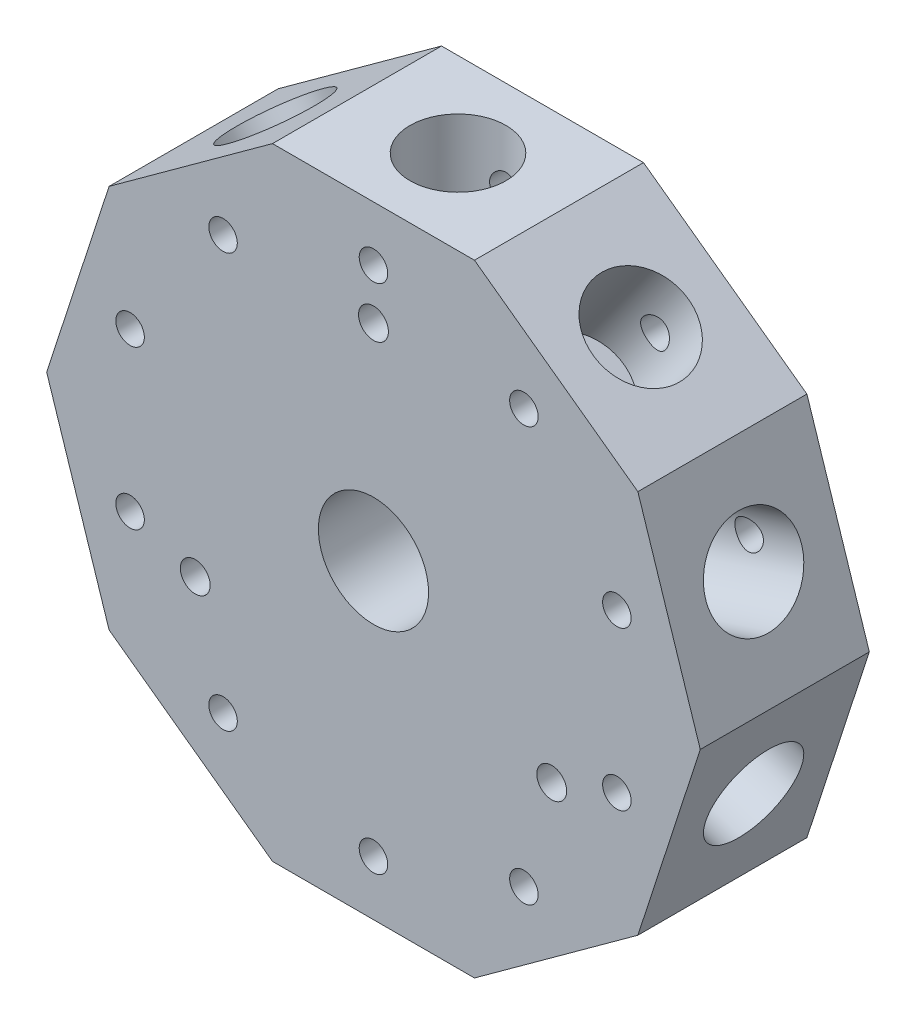
SolidWorks part; units mm, degrees
material "6061-T6 (SS)"
ref_plane "Front Plane" through (0, 0, 0) normal (0, 0, 1) x (1, 0, 0)
ref_plane "Top Plane" through (0, 0, 0) normal (0, 1, 0) x (1, 0, 0)
ref_plane "Right Plane" through (0, 0, 0) normal (1, 0, 0) x (0, 0, -1)
sketch "Sketch1" plane through (0, 0, 0) normal (0, 0, 1) x (1, 0, 0)
  line L1 (30.5891, 22.2243) -> (11.684, 35.9597)
  line L2 (11.684, 35.9597) -> (-11.684, 35.9597)
  line L3 (-11.684, 35.9597) -> (-30.5891, 22.2243)
  line L4 (-30.5891, 22.2243) -> (-37.8102, 0)
  line L5 (-37.8102, 0) -> (-30.5891, -22.2243)
  line L6 (-30.5891, -22.2243) -> (-11.684, -35.9597)
  line L7 (-11.684, -35.9597) -> (11.684, -35.9597)
  line L8 (11.684, -35.9597) -> (30.5891, -22.2243)
  line L9 (30.5891, -22.2243) -> (37.8102, 0)
  line L10 (37.8102, 0) -> (30.5891, 22.2243)
  circle A0 centre (0, 0) radius 37.8102 construction
  dimension "D1" = 23.368
extrude "Boss-Extrude1" add sketch "Sketch1" against normal blind 19.558
sketch "Sketch5" plane through (0, 35.9597, 0) normal (0, 1, 0) x (1, 0, 0)
  line L0 (11.684, 0) -> (-11.684, 0) construction
  line L1 (11.684, 19.558) -> (11.684, 0) construction
  circle A0 centre (0, 9.779) radius 5.5499
  dimension "D2" = 11.0998
  dimension "D1" = 9.779
  dimension "D3" = 11.684
extrude "Cut-Extrude3" cut sketch "Sketch5" against normal blind 12.7
sketch "Sketch6" plane through (21.1366, 29.092, 0) normal (0.5878, 0.809, 0) x (0.809, -0.5878, 0)
  line L0 (11.684, 0) -> (-11.684, 0) construction
  line L1 (11.684, 19.558) -> (11.684, 0) construction
  circle A0 centre (0, 9.779) radius 5.5499
  dimension "D2" = 11.0998
  dimension "D1" = 9.779
  dimension "D3" = 11.684
extrude "Cut-Extrude4" cut sketch "Sketch6" against normal blind 12.7
sketch "Sketch7" plane through (34.1997, 11.1121, 0) normal (0.9511, 0.309, 0) x (0, 0, -1)
  line L0 (0, -11.684) -> (0, 11.684) construction
  line L1 (19.558, -11.684) -> (0, -11.684) construction
  circle A0 centre (9.779, 0) radius 5.5499
  dimension "D2" = 11.0998
  dimension "D1" = 9.779
  dimension "D3" = 11.684
extrude "Cut-Extrude5" cut sketch "Sketch7" against normal blind 12.7
sketch "Sketch8" plane through (34.1997, -11.1121, 0) normal (0.9511, -0.309, 0) x (0, 0, -1)
  line L0 (0, -11.684) -> (0, 11.684) construction
  line L1 (19.558, -11.684) -> (0, -11.684) construction
  circle A0 centre (9.779, 0) radius 5.5499
  dimension "D2" = 11.0998
  dimension "D1" = 9.779
  dimension "D3" = 11.684
extrude "Cut-Extrude6" cut sketch "Sketch8" against normal blind 12.7
sketch "Sketch9" plane through (21.1366, -29.092, 0) normal (0.5878, -0.809, 0) x (0.809, 0.5878, 0)
  line L0 (-11.684, 0) -> (11.684, 0) construction
  line L1 (-11.684, -19.558) -> (-11.684, 0) construction
  circle A0 centre (0, -9.779) radius 5.5499
  dimension "D2" = 11.0998
  dimension "D1" = 9.779
  dimension "D3" = 11.684
extrude "Cut-Extrude7" cut sketch "Sketch9" against normal blind 12.7
sketch "Sketch10" plane through (0, -35.9597, 0) normal (0, -1, 0) x (1, 0, 0)
  line L0 (-11.684, 0) -> (11.684, 0) construction
  line L1 (-11.684, -19.558) -> (-11.684, 0) construction
  circle A0 centre (0, -9.779) radius 5.5499
  dimension "D2" = 11.0998
  dimension "D1" = 9.779
  dimension "D3" = 11.684
extrude "Cut-Extrude8" cut sketch "Sketch10" against normal blind 12.7
sketch "Sketch11" plane through (-21.1366, -29.092, 0) normal (-0.5878, -0.809, 0) x (0.809, -0.5878, 0)
  line L0 (-11.684, 0) -> (11.684, 0) construction
  line L1 (-11.684, -19.558) -> (-11.684, 0) construction
  circle A0 centre (0, -9.779) radius 5.5499
  dimension "D2" = 11.0998
  dimension "D1" = 9.779
  dimension "D3" = 11.684
extrude "Cut-Extrude9" cut sketch "Sketch11" against normal blind 12.7
sketch "Sketch12" plane through (-34.1997, -11.1121, 0) normal (-0.9511, -0.309, 0) x (0, 0, 1)
  line L0 (0, 11.684) -> (0, -11.684) construction
  line L1 (-19.558, 11.684) -> (0, 11.684) construction
  circle A0 centre (-9.779, 0) radius 5.5499
  dimension "D2" = 11.0998
  dimension "D1" = 9.779
  dimension "D3" = 11.684
extrude "Cut-Extrude10" cut sketch "Sketch12" against normal blind 12.7
sketch "Sketch13" plane through (-34.1997, 11.1121, 0) normal (-0.9511, 0.309, 0) x (0, 0, 1)
  line L0 (0, 11.684) -> (0, -11.684) construction
  line L1 (-19.558, 11.684) -> (0, 11.684) construction
  circle A0 centre (-9.779, 0) radius 5.5499
  dimension "D2" = 11.0998
  dimension "D1" = 9.779
  dimension "D3" = 11.684
extrude "Cut-Extrude11" cut sketch "Sketch13" against normal blind 12.7
sketch "Sketch14" plane through (-21.1366, 29.092, 0) normal (-0.5878, 0.809, 0) x (0.809, 0.5878, 0)
  line L0 (11.684, 0) -> (-11.684, 0) construction
  circle A0 centre (0, 9.779) radius 5.5499
  dimension "D2" = 11.0998
  dimension "D1" = 9.779
extrude "Cut-Extrude12" cut sketch "Sketch14" against normal blind 12.7
sketch "Sketch16" plane through (0, 0, 0) normal (0, 0, 1) x (1, 0, 0)
  circle A0 centre (0, 0) radius 9.525
  dimension "D1" = 19.05
extrude "Boss-Extrude2" add sketch "Sketch16" along normal blind 12.7
sketch "Sketch17" plane through (0, 0, 12.7) normal (0, 0, 1) x (1, 0, 0)
  circle A0 centre (0, 0) radius 6.3754
  dimension "D1" = 12.7508
extrude "Cut-Extrude13" cut sketch "Sketch17" against normal blind 15.24
sketch "Sketch18" plane through (0, 0, 0) normal (0, 0, 1) x (1, 0, 0)
  line L0 (11.684, 35.9597) -> (-11.684, 35.9597) construction
  circle A0 centre (0, 29.6097) radius 1.632
  circle A1 centre (17.4041, 23.9547) radius 1.632
  circle A2 centre (28.1605, 9.1499) radius 1.632
  circle A3 centre (28.1605, -9.1499) radius 1.632
  circle A4 centre (17.4041, -23.9547) radius 1.632
  circle A5 centre (0, -29.6097) radius 1.632
  circle A6 centre (-17.4041, -23.9547) radius 1.632
  circle A7 centre (-28.1605, -9.1499) radius 1.632
  circle A8 centre (-28.1605, 9.1499) radius 1.632
  circle A9 centre (-17.4041, 23.9547) radius 1.632
  circle A10 centre (0, 0) radius 9.525 construction
  point P26 (0, 0)
  dimension "D1" = 6.35
  dimension "D2" = 3.2639
  dimension "D3" = 37.8102
  dimension "D5" = 17.4041
  dimension "D4" = 10
extrude "Cut-Extrude14" cut sketch "Sketch18" against normal through all
sketch "Sketch19" plane through (0, 0, 0) normal (0, 1, 0) x (1, 0, 0)
  line L0 (-9.525, -12.7) -> (9.525, -12.7) construction
  circle A0 centre (0, -6.35) radius 1.905
  dimension "D1" = 6.35
  dimension "D2" = 3.81
extrude "Cut-Extrude15" cut sketch "Sketch19" against normal through all both and the other way through all
sketch "Sketch21" plane through (0, 0, -2.54) normal (0, 0, 1) x (1, 0, 0)
  circle A2 centre (0, 0) radius 6.3754
  circle A3 centre (0, 0) radius 6.3754
  dimension "D1" = 0
extrude "Cut-Extrude16" cut sketch "Sketch21" against normal through all
sketch "Sketch23" plane through (0, 0, 12.7) normal (0, 0, 1) x (1, 0, 0)
  circle A0 centre (0, 0) radius 9.525
extrude "Cut-Extrude17" cut sketch "Sketch23" against normal up to surface (12.7 mm away) up to face at (-15.7722, 23.9547, 0)
sketch "Sketch24" plane through (0, 0, 0) normal (0, 0, 1) x (1, 0, 0)
  circle A0 centre (0, 0) radius 23.8125 construction
  point P3 (0, 23.8125)
  point P7 (20.6222, -11.9062)
  point P8 (-20.6222, -11.9062)
  point P9 (0, 0)
  dimension "D1" = 47.625
  dimension "D2" = 3
hole_wizard "#8-32 Tapped Hole1" positions "Sketch25" profile "Sketch26" tap size "#8-32" standard "ANSI Inch" end condition through all
sketch "Sketch25" plane through (0, 0, 0) normal (0, 0, 1) x (1, 0, 0)
  point P0 (0, 23.8125)
  point P3 (20.6222, -11.9062)
  point P6 (-20.6222, -11.9062)
sketch "Sketch26" plane through (0, 23.8125, 0) normal (1, 0, 0) x (0, -1, 0)
  line L0 (0, 0) -> (0, 19.558)
  line L1 (0, 19.558) -> (1.7272, 19.558)
  line L2 (1.7272, 19.558) -> (1.7272, 0)
  line L5 (1.7272, 0) -> (0, 0)
  line L11 (0, -6.35) -> (0, 107.95) construction
  dimension "Thru Tap Drill Dia." = 3.4544
  dimension "Thru Tap Drill Depth" = 19.558
cosmetic thread "Hole Thread1" parameters "D2"=4.1656
cosmetic thread "Hole Thread2" parameters "D2"=4.1656
cosmetic thread "Hole Thread3" parameters "D2"=4.1656
hole_wizard "M4x0.7 Tapped Hole1" positions "Sketch27" profile "Sketch28" tap size "M4x0.7" standard "ANSI Metric" end condition up to next
sketch "Sketch27" plane through (0, 0, 0) normal (0, 0, 1) x (1, 0, 0)
  point P0 (-17.4041, 23.9547)
  point P3 (-28.1605, 9.1499)
  point P6 (-28.1605, -9.1499)
  point P9 (-17.4041, -23.9547)
  point P12 (0, -29.6097)
  point P15 (17.4041, -23.9547)
  point P18 (28.1605, -9.1499)
  point P21 (28.1605, 9.1499)
  point P24 (17.4041, 23.9547)
  point P27 (0, 29.6097)
sketch "Sketch28" plane through (-17.4041, 23.9547, 0) normal (1, 0, 0) x (0, -1, 0)
  line L0 (0, 0) -> (0, 19.558)
  line L1 (0, 19.558) -> (1.65, 19.558)
  line L2 (1.65, 19.558) -> (1.65, 0)
  line L5 (1.65, 0) -> (0, 0)
  line L11 (0, -6.35) -> (0, 107.95) construction
  dimension "Thru Tap Drill Dia." = 3.3
  dimension "Thru Tap Drill Depth" = 19.558
cosmetic thread "Hole Thread4" parameters "D2"=4
cosmetic thread "Hole Thread5" parameters "D2"=4
cosmetic thread "Hole Thread6" parameters "D2"=4
cosmetic thread "Hole Thread7" parameters "D2"=4
cosmetic thread "Hole Thread8" parameters "D2"=4
cosmetic thread "Hole Thread9" parameters "D2"=4
cosmetic thread "Hole Thread10" parameters "D2"=4
cosmetic thread "Hole Thread11" parameters "D2"=4
cosmetic thread "Hole Thread12" parameters "D2"=4
cosmetic thread "Hole Thread13" parameters "D2"=4
